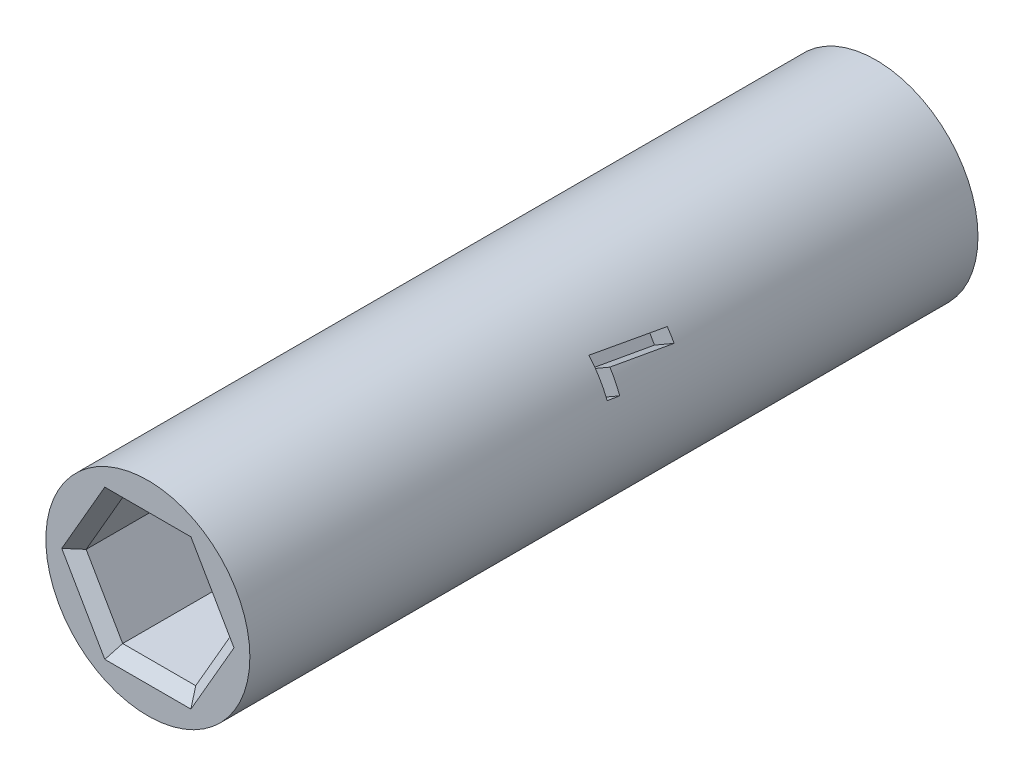
SolidWorks part; units mm, degrees
ref_plane "Front Plane" through (0, 0, 0) normal (0, 0, 1) x (1, 0, 0)
ref_plane "Top Plane" through (0, 0, 0) normal (0, 1, 0) x (1, 0, 0)
ref_plane "Right Plane" through (0, 0, 0) normal (1, 0, 0) x (0, 0, -1)
sketch "Sketch1" plane through (0, 0, 0) normal (0, 1, 0) x (1, 0, 0)
  line L0 (0, 0) -> (0, 67.1171) construction
  line L1 (0, 49.6171) -> (0, 17.5)
  point P3 (0, 43.1171)
  point P4 (0, 24)
  point P5 (0, 49.6171)
  point P6 (0, 17.5)
  dimension "D1" = 67.1171
  dimension "D2" = 24
  dimension "D3" = 24
  dimension "D4" = 19.1171
  dimension "D5" = 6.5
  dimension "D6" = 6.5
revolve "Revolve-Thin1" add sketch "Sketch1" angle 360 about L0 wall 4.5
sketch "Sketch2" plane through (0, 0, -17.5) normal (0, 0, 1) x (1, 0, 0)
  line L1 (1.6108, 2.79) -> (-1.6108, 2.79)
  line L2 (-1.6108, 2.79) -> (-3.2216, 0)
  line L3 (-3.2216, 0) -> (-1.6108, -2.79)
  line L4 (-1.6108, -2.79) -> (1.6108, -2.79)
  line L5 (1.6108, -2.79) -> (3.2216, 0)
  line L6 (3.2216, 0) -> (1.6108, 2.79)
  circle A0 centre (0, 0) radius 2.79 construction
  dimension "D1" = 5.58
extrude "Cut-Extrude1" cut sketch "Sketch2" against normal blind 7
sketch "Sketch3" plane through (0, 0, -49.6171) normal (0, 0, -1) x (-1, 0, 0)
  line L1 (1.6108, 2.79) -> (-1.6108, 2.79)
  line L2 (-1.6108, 2.79) -> (-3.2216, 0)
  line L3 (-3.2216, 0) -> (-1.6108, -2.79)
  line L4 (-1.6108, -2.79) -> (1.6108, -2.79)
  line L5 (1.6108, -2.79) -> (3.2216, 0)
  line L6 (3.2216, 0) -> (1.6108, 2.79)
  circle A0 centre (0, 0) radius 2.79 construction
  dimension "D1" = 5.58
extrude "Cut-Extrude2" cut sketch "Sketch3" against normal blind 7
chamfer "Chamfer1" distance 0.5 angle 45 12 edges at (2.4162, 1.395, -17.5) (2.4162, -1.395, -17.5) (0, -2.79, -17.5) (-2.4162, -1.395, -17.5) (-2.4162, 1.395, -17.5) (0, 2.79, -17.5) (0, 2.79, -49.6171) (-2.4162, 1.395, -49.6171) (-2.4162, -1.395, -49.6171) (0, -2.79, -49.6171) (2.4162, -1.395, -49.6171) (2.4162, 1.395, -49.6171)
sketch3d "3DSketch1" plane through (0, 0, 0) normal (0, 0, 1) x (1, 0, 0)
sketch "Sketch4" plane through (3.8971, 2.25, 0) normal (0.866, 0.5, 0) x (0, 0, -1)
  line L0 (49.6171, -4.5) -> (49.6171, 4.5) construction
  line L1 (49.6171, -4.5) -> (49.6171, 4.5) construction
  line L2 (0, 0) -> (49.6171, 0) construction
  line L3 (17.5, 4.5) -> (17.5, -4.5) construction
  line L4 (17.5, 4.5) -> (17.5, -4.5) construction
  line L5 (17.5, 4.5) -> (49.6171, 4.5) construction
  line L6 (33.5585, 4.5) -> (33.5585, -4.5) construction
  line L7 (17.5, -4.5) -> (49.6171, -4.5) construction
  text T0 "<b><i>L</i></b>"
extrude "Cut-Extrude3" cut sketch "Sketch4" against normal blind 1
